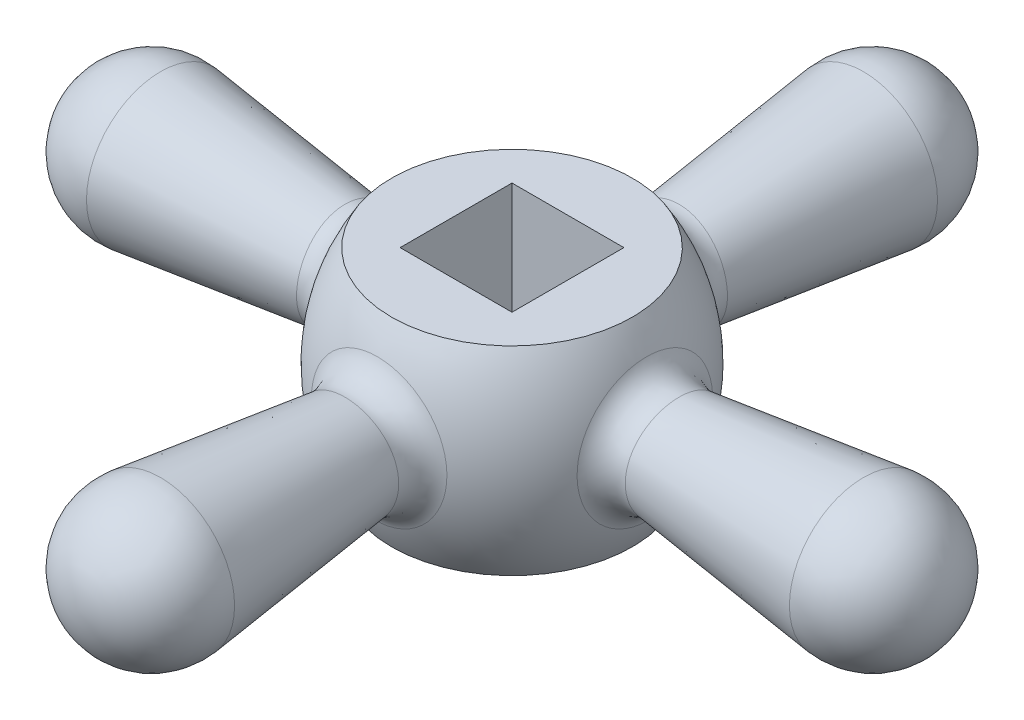
SolidWorks part; units mm, degrees
ref_plane "Front Plane" through (0, 0, 0) normal (0, 0, 1) x (1, 0, 0)
ref_plane "Top Plane" through (0, 0, 0) normal (0, 1, 0) x (1, 0, 0)
ref_plane "Right Plane" through (0, 0, 0) normal (1, 0, 0) x (0, 0, -1)
sketch "Sketch1" plane through (0, 0, 0) normal (0, 0, 1) x (1, 0, 0)
  line L0 (0, 7.8302) -> (0, -8.1698)
  line L1 (0, 7.8302) -> (-9.6886, 7.8302)
  line L2 (0, -8.1698) -> (-9.6886, -8.1698)
  arc A0 (-9.6886, 7.8302) -> (-9.6886, -8.1698) centre (3, -0.1698) ccw
  point P6 (0, 0)
  point P7 (-12, -0.1698)
  dimension "D2" = 15
  dimension "D3" = 12
  dimension "D1" = 16
revolve "Revolve1" add sketch "Sketch1" angle 360 about L0
sketch "Sketch2" plane through (0, 0, 0) normal (0, 0, 1) x (1, 0, 0)
  line L0 (0, 0) -> (-35, 0)
  line L2 (-28.2688, -5.9553) -> (0, -2.4843)
  line L3 (0, 0) -> (0, -2.4843)
  arc A0 (-35, 0) -> (-28.2688, -5.9553) centre (-29, 0) ccw
  point P5 (0, 0)
  dimension "D3" = 6
  dimension "D1" = 35
  dimension "D2" = 7
revolve "Revolve2" add sketch "Sketch2" angle 360 about L0
fillet "Fillet1" radius 2.5 1 edges at (-11.4099, 3.2908, 2.0654)
pattern_circular "CirPattern3" count 4 over 360 about axis through (0, 7.8302, 0) along (0, 1, 0) of "Revolve2", "Fillet1"
sketch "Sketch3" plane through (0, 7.8302, 0) normal (0, 1, 0) x (1, 0, 0)
  line L1 (4.5, -4.5) -> (-4.5, -4.5)
  line L2 (4.5, -4.5) -> (4.5, 4.5)
  line L3 (4.5, 4.5) -> (-4.5, 4.5)
  line L4 (-4.5, -4.5) -> (-4.5, 4.5)
  line L5 (4.5, -4.5) -> (-4.5, 4.5) construction
  line L6 (4.5, 4.5) -> (-4.5, -4.5) construction
  point P0 (0, 0)
  dimension "D1" = 9
extrude "Cut-Extrude1" cut sketch "Sketch3" against normal blind 11
